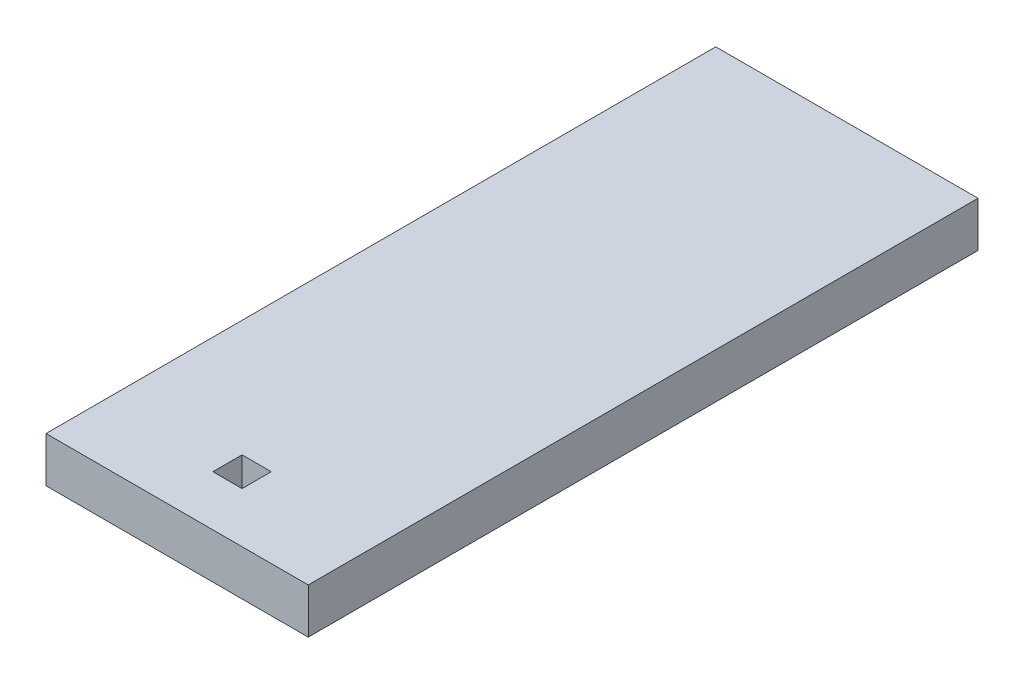
SolidWorks part; units mm, degrees
ref_plane "Front Plane" through (0, 0, 0) normal (0, 0, 1) x (1, 0, 0)
ref_plane "Top Plane" through (0, 0, 0) normal (0, 1, 0) x (1, 0, 0)
ref_plane "Right Plane" through (0, 0, 0) normal (1, 0, 0) x (0, 0, -1)
sketch "Sketch1" plane through (0, 0, 0) normal (0, 1, 0) x (1, 0, 0)
  line L0 (0, 23.495) -> (0, 0) construction
  line L1 (-9.2, 23.495) -> (9.2, 23.495)
  line L2 (-9.2, 23.495) -> (-9.2, -23.495)
  line L3 (-9.2, -23.495) -> (9.2, -23.495)
  line L4 (9.2, 23.495) -> (9.2, -23.495)
  line L5 (0, -17.9142) -> (0, 0) construction
  line L6 (-1.025, -17.9142) -> (1.025, -17.9142)
  line L7 (-1.025, -17.9142) -> (-1.025, -19.9642)
  line L8 (-1.025, -19.9642) -> (1.025, -19.9642)
  line L9 (1.025, -17.9142) -> (1.025, -19.9642)
  line L11 (-9.2, 23.495) -> (-12.375, 23.495)
  line L12 (-9.2, 23.495) -> (-9.2, -23.495)
  line L13 (-9.2, -23.495) -> (-12.375, -23.495)
  line L14 (-12.375, 23.495) -> (-12.375, -23.495)
  point P14 (9.2, 0)
  dimension "D1" = 18.4
  dimension "D2" = 46.99
  dimension "D3" = 3.5308
  dimension "D4" = 2.05
  dimension "D5" = 3.175
extrude "Boss-Extrude1" add sketch "Sketch1" along normal blind 3.175 contours L4 L1 L2 L3 L6 L9 L8 L7 | L11 L14 L13 L2
sketch "Sketch2" plane through (0, 3.175, 0) normal (0, 1, 0) x (1, 0, 0)
  line L0 (-12.375, -23.495) -> (9.2, -23.495) construction
  line L1 (-12.375, 23.495) -> (-9.2, 23.495)
  line L2 (-12.375, 23.495) -> (-12.375, -23.495)
  line L3 (-12.375, -23.495) -> (-9.2, -23.495)
  line L4 (-9.2, 23.495) -> (-9.2, -23.495)
  dimension "D1" = 3.175
extrude "Cut-Extrude1" cut sketch "Sketch2" against normal through all
equation "\"bottomThickness\"= .220in"
equation "\"wallThickness\"= .125in"
equation "\"D1@Sketch2\"=\"wallThickness\""
equation "\"D1@Boss-Extrude1\"=\"wallThickness\""
